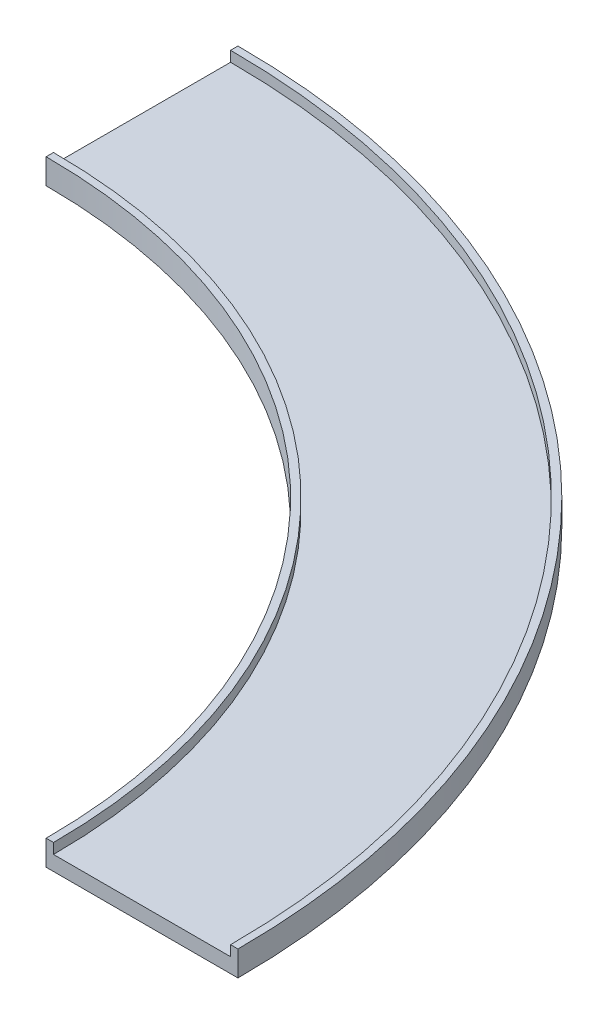
SolidWorks part; units mm, degrees
ref_plane "Front Plane" through (0, 0, 0) normal (0, 0, 1) x (1, 0, 0)
ref_plane "Top Plane" through (0, 0, 0) normal (0, 1, 0) x (1, 0, 0)
ref_plane "Right Plane" through (0, 0, 0) normal (1, 0, 0) x (0, 0, -1)
sketch "Sketch1" plane through (0, 0, 0) normal (0, 0, 1) x (1, 0, 0)
  line L0 (0, 0) -> (25, 0)
  line L1 (25, 0) -> (25, -35.2361)
  line L2 (25, -35.2361) -> (625, -35.2361)
  line L3 (625, -35.2361) -> (625, 0)
  line L4 (625, 0) -> (650, 0)
  line L5 (650, 0) -> (650, -85.2361)
  line L6 (650, -85.2361) -> (0, -85.2361)
  line L7 (0, -85.2361) -> (0, 0)
  line L8 (-2000, 0) -> (-2000, 547.1361)
  dimension "D1" = 25
  dimension "D2" = 35.2361
  dimension "D3" = 650
  dimension "D4" = 50
  dimension "D5" = 2000
revolve "Revolve3" add sketch "Sketch1" angle 90 about L8
